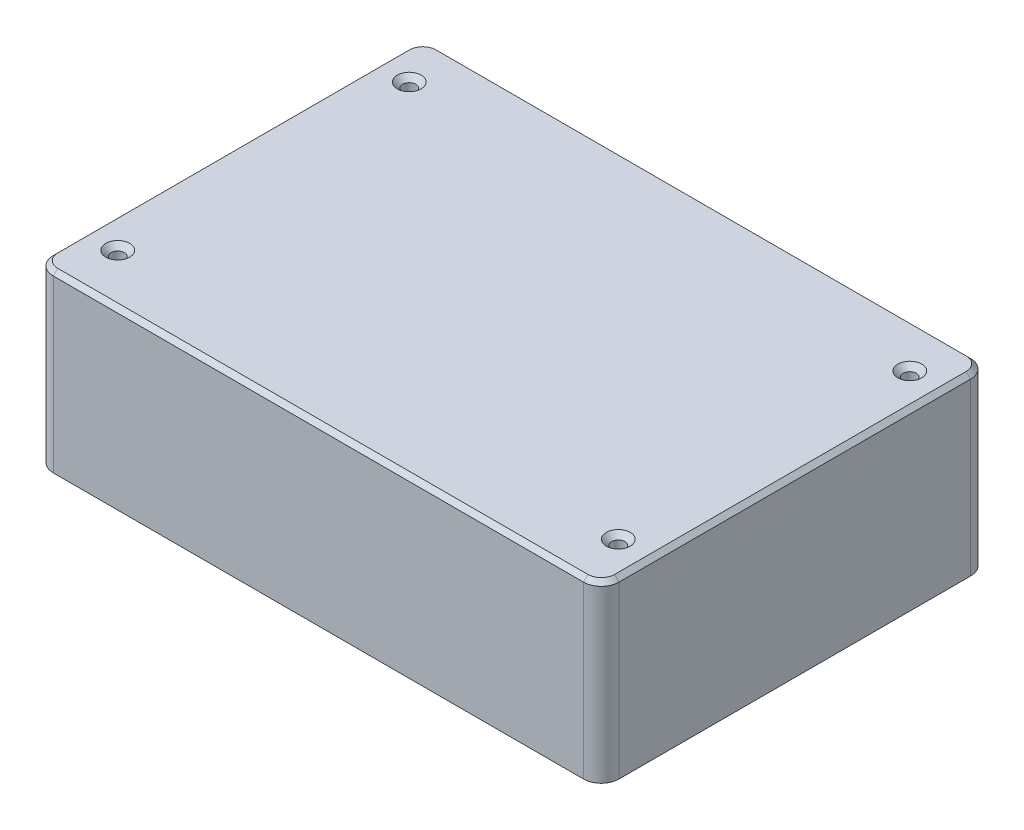
SolidWorks part; units mm, degrees
other "Markup1"
sketch "Sketch8" plane through (-63.85, 0, -43.7) normal (-0.8076, -0.505, -0.3045) x (-0.4864, 0.8624, -0.1401)
ref_plane "Front Plane" through (0, 0, 0) normal (0, 0, 1) x (1, 0, 0)
ref_plane "Top Plane" through (0, 0, 0) normal (0, 1, 0) x (1, 0, 0)
ref_plane "Right Plane" through (0, 0, 0) normal (1, 0, 0) x (0, 0, -1)
sketch "Sketch1" plane through (0, 0, 0) normal (0, 1, 0) x (1, 0, 0)
  line L1 (63.85, 43.7) -> (-63.85, 43.7)
  line L2 (63.85, 43.7) -> (63.85, -43.7)
  line L3 (63.85, -43.7) -> (-63.85, -43.7)
  line L4 (-63.85, 43.7) -> (-63.85, -43.7)
  line L5 (63.85, 43.7) -> (-63.85, -43.7) construction
  line L6 (63.85, -43.7) -> (-63.85, 43.7) construction
  point P0 (0, 0)
  dimension "D1" = 87.4
  dimension "D2" = 127.7
extrude "Boss-Extrude1" add sketch "Sketch1" along normal blind 39.5
shell "Shell1" thickness 3
fillet "Fillet2" radius 4 4 edges at (63.85, 19.75, -43.7) (-63.85, 19.75, -43.7) (-63.85, 19.75, 43.7) (63.85, 19.75, 43.7)
hole_wizard "CSK for M2 Flat Head Machine Screw3" positions "3DSketch3" profile "Sketch6" countersink size "M2" standard "ANSI Metric" end condition through all
sketch3d "3DSketch3"
  line L0 (63.85, 39.5, 39.7) -> (63.85, 39.5, -39.7) construction
  line L1 (-59.85, 39.5, 43.7) -> (59.85, 39.5, 43.7) construction
  line L2 (59.85, 39.5, -43.7) -> (-59.85, 39.5, -43.7) construction
  point P0 (56.4, 39.5, -33.4)
  point P2 (-56.6, 39.5, -33.4)
  point P4 (-56.6, 39.5, 32.4)
  point P6 (56.4, 39.5, 32.4)
  dimension "D1" = 7.45
  dimension "D2" = 65.8
  dimension "D3" = 11.3
  dimension "D4" = 10.3
  dimension "D5" = 113
  dimension "D6" = 65.8
  dimension "D7" = 113
  dimension "D8" = 11.3
sketch "Sketch6" plane through (56.4, 39.5, -33.4) normal (1, 0, 0) x (0, 0, 1)
  line L0 (0, 0) -> (0, 39.5)
  line L1 (0, 39.5) -> (1.5, 39.5)
  line L2 (1.5, 39.5) -> (1.5, 1.2)
  line L3 (1.5, 1.2) -> (2.7, 0)
  line L5 (2.7, 0) -> (0, 0)
  line L6 (-1.5, 1.2) -> (-2.7, 0) construction
  line L11 (0, -6.35) -> (0, 107.95) construction
  dimension "Thru Hole Dia." = 3
  dimension "Thru Hole Depth" = 39.5
  dimension "Near C'Sink Dia." = 5.4
  dimension "Near C'Sink Angle" = 90
sketch "Sketch9" plane through (0, 0, -43.7) normal (0, 0, -1) x (-1, 0, 0)
  line L0 (-27.2, 18.36) -> (-22.5, 18.36) construction
  line L3 (-27.2, 22.11) -> (-22.5, 22.11)
  line L4 (-27.2, 14.61) -> (-22.5, 14.61)
  line L5 (-63.85, 0) -> (-63.85, 39.5) construction
  line L6 (-59.85, 0) -> (59.85, 0) construction
  arc A2 (-27.2, 22.11) -> (-27.2, 14.61) centre (-27.2, 18.36) ccw
  arc A3 (-22.5, 14.61) -> (-22.5, 22.11) centre (-22.5, 18.36) ccw
  point P2 (-24.85, 18.36)
  dimension "D1" = 39
  dimension "D2" = 18.36
extrude "Cut-Extrude1" cut sketch "Sketch9" against normal up to next
chamfer "Chamfer1" distance 1 angle 45 8 edges at (30.95, 18.36, -40.7) (24.85, 14.61, -40.7) (18.75, 18.36, -40.7) (24.85, 22.11, -40.7) (24.85, 22.11, -43.7) (30.95, 18.36, -43.7) (24.85, 14.61, -43.7) (18.75, 18.36, -43.7)
chamfer "Chamfer2" distance 1 angle 45 8 edges at (62.6784, 39.5, -42.5284) (63.85, 39.5, 0) (62.6784, 39.5, 42.5284) (0, 39.5, 43.7) (-62.6784, 39.5, 42.5284) (-63.85, 39.5, 0) (-62.6784, 39.5, -42.5284) (0, 39.5, -43.7)
chamfer "Chamfer3" distance 1 angle 45 8 edges at (-60.85, 18.25, -40.7) (60.85, 18.25, 40.7) (60.85, 18.25, -40.7) (0, 36.5, -40.7) (60.85, 36.5, 0) (0, 36.5, 40.7) (-60.85, 36.5, 0) (-60.85, 18.25, 40.7)
